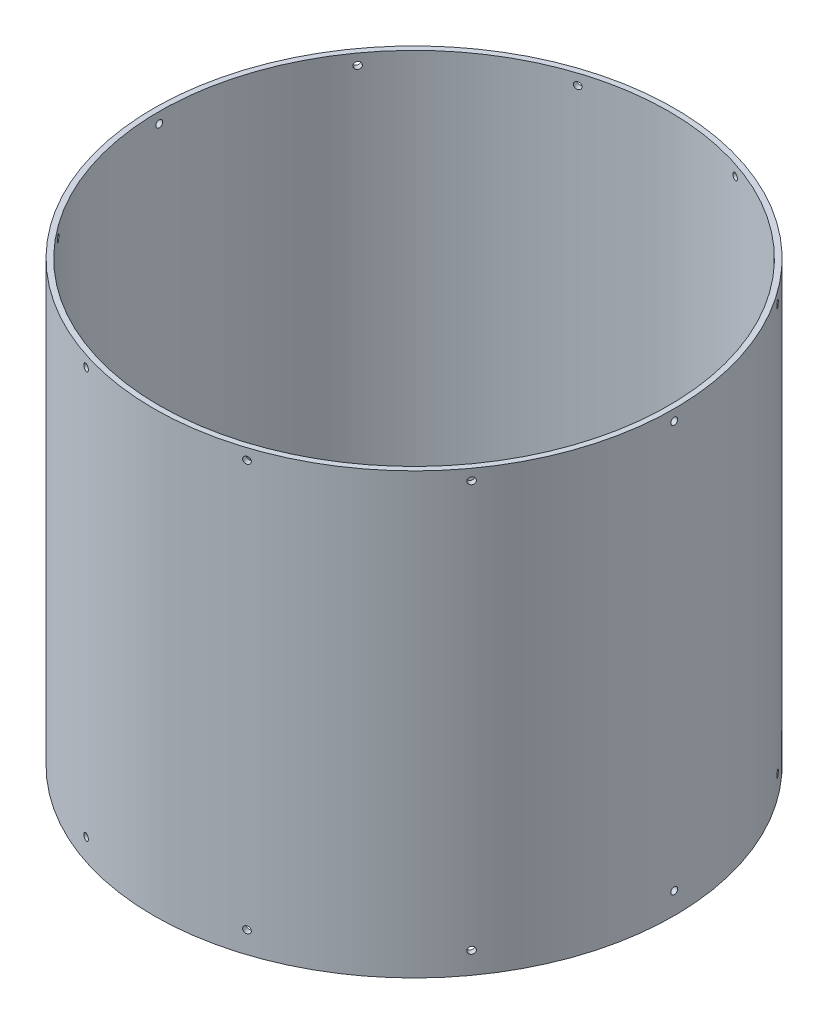
SolidWorks part; units mm, degrees
material "Hexcel AS4C (3000 Filaments)"
ref_plane "Front Plane" through (0, 0, 0) normal (0, 0, 1) x (1, 0, 0)
ref_plane "Top Plane" through (0, 0, 0) normal (0, 1, 0) x (1, 0, 0)
ref_plane "Right Plane" through (0, 0, 0) normal (1, 0, 0) x (0, 0, -1)
sketch "Sketch1" plane through (0, 0, 0) normal (0, 1, 0) x (1, 0, 0)
  circle A0 centre (0, 0) radius 152.4
  circle A1 centre (0, 0) radius 149.225
  dimension "D1" = 304.8
  dimension "D2" = 3.175
extrude "Boss-Extrude1" add sketch "Sketch1" along normal blind 257.175
ref_plane "Plane1" through (152.4, 0, 0) normal (1, 0, 0) x (0, 0, -1)
sketch "Sketch2" plane through (152.4, 0, 0) normal (1, 0, 0) x (0, 0, -1)
  line L0 (0, 323.4357) -> (0, -45.9614) construction
  line L1 (-152.4, 0) -> (152.4, 0) construction
  line L2 (152.4, 257.175) -> (-152.4, 257.175) construction
  line L3 (-152.4, 0) -> (152.4, 0) construction
  line L4 (152.4, 257.175) -> (-152.4, 257.175) construction
hole_wizard "#10-32 Tapped Hole1" positions "3DSketch1" profile "Sketch3" tap size "#10-32" standard "ANSI Inch"
sketch3d "3DSketch1"
  line L0 (152.4, 323.4357, 0) -> (152.4, -45.9614, 0) construction
  line L1 (152.4, 257.175, -152.4) -> (152.4, 257.175, 152.4) construction
  line L2 (152.4, 0, 152.4) -> (152.4, 0, -152.4) construction
  point P0 (152.4, 250.825, 0)
  point P2 (152.4, 12.7, 0)
  dimension "D1" = 6.35
  dimension "D2" = 12.7
sketch "Sketch3" plane through (152.4, 250.825, 0) normal (0, 1, 0) x (0, 0, -1)
  line L0 (0, 0) -> (0, 360.8392)
  line L1 (0, 360.8392) -> (2.0193, 360.8392)
  line L2 (2.0193, 360.8392) -> (2.0193, 0)
  line L5 (2.0193, 0) -> (0, 0)
  line L11 (0, -6.35) -> (0, 107.95) construction
  dimension "Thru Tap Drill Dia." = 4.0386
  dimension "Thru Tap Drill Depth" = 360.8392
cosmetic thread "Hole Thread1" parameters "D2"=4.826
cosmetic thread "Hole Thread2" parameters "D2"=4.826
pattern_circular "CirPattern1" count 10 over 360 about axis through (0, 257.175, 0) along (0, -1, 0) of "#10-32 Tapped Hole1"
